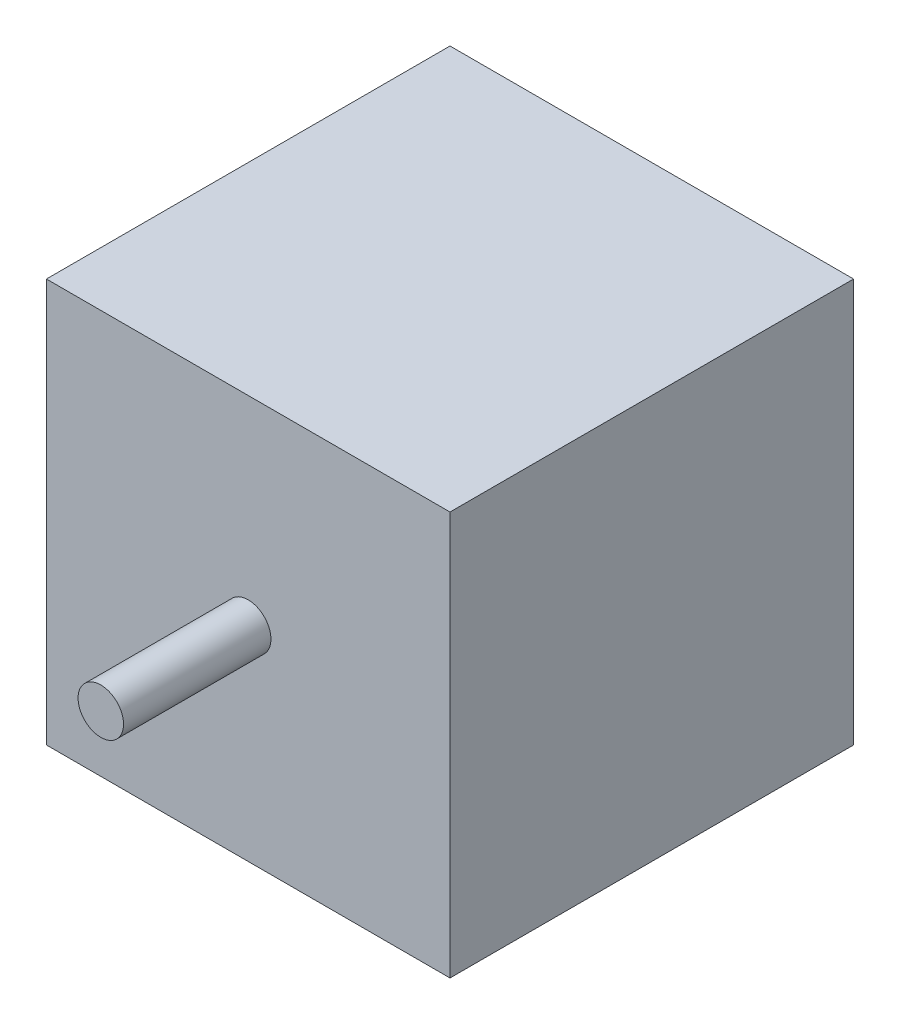
SolidWorks part; units mm, degrees
ref_plane "Front Plane" through (0, 0, 0) normal (0, 0, 1) x (1, 0, 0)
ref_plane "Top Plane" through (0, 0, 0) normal (0, 1, 0) x (1, 0, 0)
ref_plane "Right Plane" through (0, 0, 0) normal (1, 0, 0) x (0, 0, -1)
sketch "Sketch1" plane through (0, 0, 0) normal (0, 1, 0) x (1, 0, 0)
  line L1 (28.2, -28.2) -> (-28.2, -28.2)
  line L2 (28.2, -28.2) -> (28.2, 28.2)
  line L3 (28.2, 28.2) -> (-28.2, 28.2)
  line L4 (-28.2, -28.2) -> (-28.2, 28.2)
  line L5 (28.2, -28.2) -> (-28.2, 28.2) construction
  line L6 (28.2, 28.2) -> (-28.2, -28.2) construction
  point P0 (0, 0)
  dimension "D1" = 56.3999
  dimension "D2" = 56.3999
extrude "Boss-Extrude1" add sketch "Sketch1" along normal blind 56.3999
sketch "Sketch2" plane through (0, 0, 28.2) normal (0, 0, 1) x (1, 0, 0)
  circle A0 centre (0, 28.4953) radius 3.175
extrude "Boss-Extrude2" add sketch "Sketch2" along normal blind 20.6
